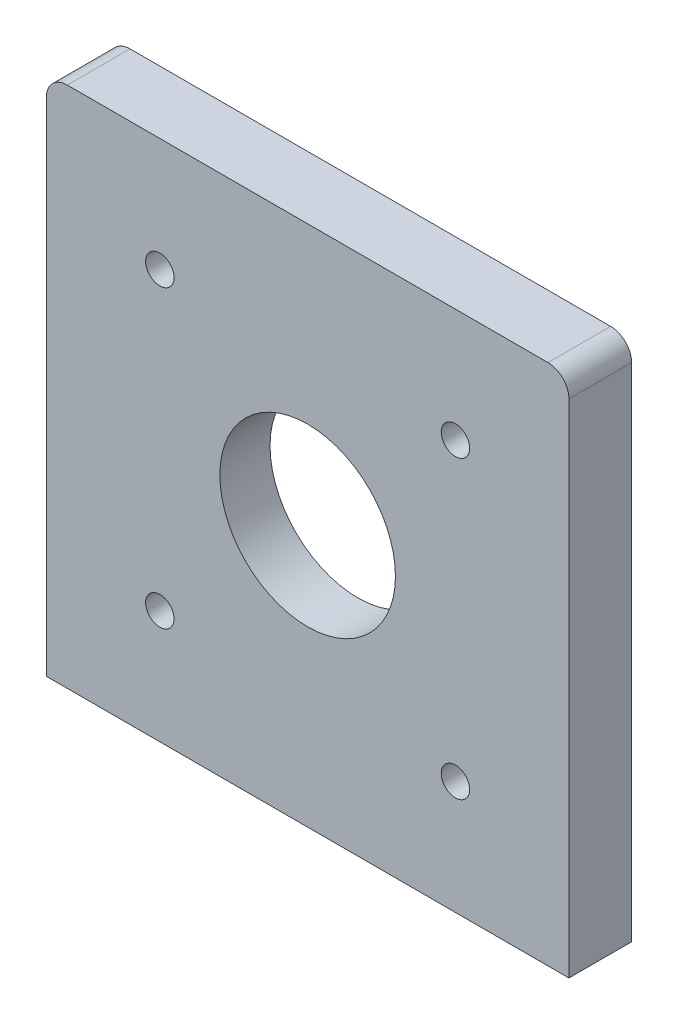
SolidWorks part; units mm, degrees
ref_plane "Plan de face" through (0, 0, 0) normal (0, 0, 1) x (1, 0, 0)
ref_plane "Plan de dessus" through (0, 0, 0) normal (0, 1, 0) x (1, 0, 0)
ref_plane "Plan de droite" through (0, 0, 0) normal (1, 0, 0) x (0, 0, -1)
sketch "Esquisse1" plane through (0, 0, 0) normal (0, 0, 1) x (1, 0, 0)
  line L1 (0, 0) -> (-125, 0)
  line L2 (0, 0) -> (0, 125)
  line L3 (0, 125) -> (-125, 125)
  line L4 (-125, 0) -> (-125, 125)
  dimension "D1" = 125
  dimension "D2" = 125
extrude "Boss.-Extru.1" add sketch "Esquisse1" along normal blind 15
sketch "Esquisse2" plane through (0, 0, 0) normal (0, 0, -1) x (-1, 0, 0)
  line L0 (0, 125) -> (125, 125) construction
  line L1 (125, 125) -> (125, 0) construction
  circle A1 centre (62.5, 62.5) radius 40
  dimension "D1" = 62.5
  dimension "D2" = 62.5
extrude "Enlèv. mat.-Extru.1" cut sketch "Esquisse2" against normal blind 3
fillet "Congé1" radius 5 2 edges at (-125, 125, 7.5) (0, 125, 7.5)
sketch "Esquisse11" plane through (0, 0, 3) normal (0, 0, -1) x (-1, 0, 0)
  circle A0 centre (62.5, 62.5) radius 21
extrude "Enlèv. mat.-Extru.2" cut sketch "Esquisse11" against normal blind 15
hole_wizard "Trou taraudé M81" positions "Esquisse13" profile "Esquisse12" tap size "M8" standard "ISO"
sketch "Esquisse13" plane through (0, 0, 0) normal (0, 0, -1) x (-1, 0, 0)
  point P0 (97.8553, 97.8553)
  point P3 (27.1447, 97.8553)
  point P6 (27.1447, 27.1447)
  point P9 (97.8553, 27.1447)
sketch "Esquisse12" plane through (-97.8553, 97.8553, 0) normal (1, 0, 0) x (0, 1, 0)
  line L0 (0, 0) -> (0, 24.2929)
  line L1 (0, 24.2929) -> (3.4, 22.25)
  line L2 (3.4, 22.25) -> (3.4, 0)
  line L5 (3.4, 0) -> (0, 0)
  line L10 (0, 24.2929) -> (-3.4, 22.25) construction
  line L11 (0, -6.35) -> (0, 107.95) construction
  dimension "Diamètre du trou pour taraudage" = 6.8
  dimension "Profondeur du trou pour taraudage" = 22.25
  dimension "Angle de pointe" = 118
cosmetic thread "Filetage de perçage1" parameters "D1"=15, "D2"=8
cosmetic thread "Filetage de perçage2" parameters "D1"=15, "D2"=8
cosmetic thread "Filetage de perçage3" parameters "D1"=15, "D2"=8
cosmetic thread "Filetage de perçage4" parameters "D1"=15, "D2"=8
